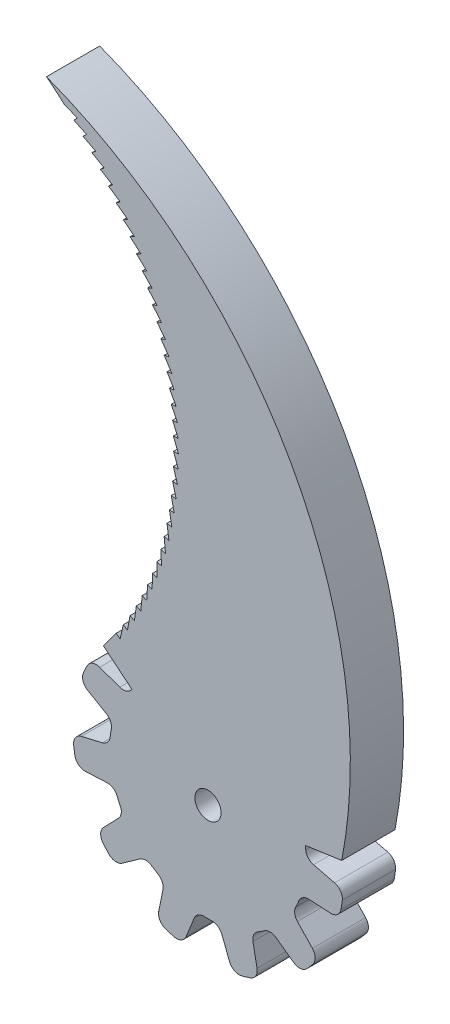
SolidWorks part; units mm, degrees
ref_plane "Plano frontal" through (0, 0, 0) normal (0, 0, 1) x (1, 0, 0)
ref_plane "Plano superior" through (0, 0, 0) normal (0, 1, 0) x (1, 0, 0)
ref_plane "Plano direito" through (0, 0, 0) normal (1, 0, 0) x (0, 0, -1)
sketch "Esboço1" plane through (0, 0, 0) normal (0, 0, 1) x (1, 0, 0)
  line L0 (-1.7292, 15.3638) -> (-1.9869, 12.7283)
  line L1 (6.8516, 13.8597) -> (5.2099, 11.782)
  line L2 (9.7799, 11.9607) -> (8.5606, 9.6439)
  line L3 (1.761, 15.3494) -> (1.9878, 12.7412)
  line L4 (13.2571, 7.9553) -> (10.7527, 7.0949)
  line L5 (14.6938, 4.7745) -> (12.4156, 3.4848)
  line L6 (15.4535, -0.4749) -> (12.8816, 0.1553)
  line L7 (14.9425, -3.9275) -> (12.3286, -3.7808)
  line L8 (12.7436, -8.7543) -> (10.9206, -6.8337)
  line L9 (10.4471, -11.3826) -> (8.3275, -9.846)
  line L10 (5.9876, -14.2543) -> (5.4924, -11.653)
  line L11 (2.6348, -15.2238) -> (1.6824, -12.7851)
  line L12 (-2.6693, -15.2286) -> (-1.6795, -12.7725)
  line L13 (-6.0141, -14.2315) -> (-5.4969, -11.6651)
  line L14 (-10.4788, -11.368) -> (-8.3183, -9.8369)
  line L15 (-12.7535, -8.7209) -> (-10.9309, -6.8415)
  line L16 (-14.9613, -3.8981) -> (-12.316, -3.7781)
  line L17 (-15.4438, -0.4414) -> (-12.8944, 0.1543)
  line L18 (-14.6937, 4.8094) -> (-12.4035, 3.4802)
  line L19 (-13.2308, 7.9782) -> (-10.7641, 7.101)
  line L20 (-9.761, 11.99) -> (-8.553, 9.6335)
  line L21 (-6.8171, 13.8648) -> (-5.2162, 11.7933)
  circle A0 centre (0, 0) radius 1.6
  arc A1 (1.9878, 12.7412) -> (2.9281, 11.6373) centre (3.2331, 12.8495) ccw
  arc A2 (0.558, 16.4904) -> (-0.5249, 16.4915) centre (0, 0) ccw
  arc A3 (0.558, 16.4904) -> (1.761, 15.3494) centre (0.5157, 15.2411) cw
  arc A4 (-0.5249, 16.4915) -> (-1.7292, 15.3638) centre (-0.4851, 15.2421) ccw
  arc A5 (-1.9869, 12.7283) -> (-2.9262, 11.6378) centre (-3.231, 12.85) cw
  arc A6 (8.5606, 9.6439) -> (8.7548, 8.2069) centre (9.6668, 9.0618) ccw
  arc A7 (9.3848, 13.571) -> (8.4744, 14.1573) centre (0, 0) ccw
  arc A8 (9.3848, 13.571) -> (9.7799, 11.9607) centre (8.6738, 12.5428) cw
  arc A9 (8.4744, 14.1573) -> (6.8516, 13.8597) centre (7.8324, 13.0848) ccw
  arc A10 (5.2099, 11.782) -> (3.8302, 11.3723) centre (4.2292, 12.5569) cw
  arc A11 (12.4156, 3.4848) -> (11.802, 2.1708) centre (13.0314, 2.397) ccw
  arc A12 (15.232, 6.3428) -> (14.7831, 7.3283) centre (0, 0) ccw
  arc A13 (15.232, 6.3428) -> (14.6938, 4.7745) centre (14.078, 5.8623) cw
  arc A14 (14.7831, 7.3283) -> (13.2571, 7.9553) centre (13.6632, 6.7731) ccw
  arc A15 (10.7527, 7.0949) -> (9.3705, 7.4963) centre (10.3466, 8.2771) cw
  arc A16 (12.3286, -3.7808) -> (11.1021, -4.5544) centre (12.2586, -5.0288) ccw
  arc A17 (16.2431, -2.8991) -> (16.3983, -1.8274) centre (0, 0) ccw
  arc A18 (16.2431, -2.8991) -> (14.9425, -3.9275) centre (15.0126, -2.6795) cw
  arc A19 (16.3983, -1.8274) -> (15.4535, -0.4749) centre (15.156, -1.689) ccw
  arc A20 (12.8816, 0.1553) -> (11.9357, 1.2402) centre (13.179, 1.3694) cw
  arc A21 (8.3275, -9.846) -> (6.8774, -9.8337) centre (7.5938, -10.858) ccw
  arc A22 (12.0972, -11.2206) -> (12.8072, -10.403) centre (0, 0) ccw
  arc A23 (12.0972, -11.2206) -> (10.4471, -11.3826) centre (11.1808, -10.3705) cw
  arc A24 (12.8072, -10.403) -> (12.7436, -8.7543) centre (11.8369, -9.6148) ccw
  arc A25 (10.9206, -6.8337) -> (10.7115, -5.4096) centre (11.8273, -5.9731) cw
  arc A26 (1.6824, -12.7851) -> (0.4691, -11.9908) centre (0.518, -13.2399) ccw
  arc A27 (4.1105, -15.9796) -> (5.1498, -15.6756) centre (0, 0) ccw
  arc A28 (4.1105, -15.9796) -> (2.6348, -15.2238) centre (3.7991, -14.769) cw
  arc A29 (5.1498, -15.6756) -> (5.9876, -14.2543) centre (4.7597, -14.488) ccw
  arc A30 (5.4924, -11.653) -> (6.0864, -10.3419) centre (6.7204, -11.4192) cw
  arc A31 (-5.4969, -11.6651) -> (-6.0881, -10.341) centre (-6.7222, -11.4181) ccw
  arc A32 (-5.1812, -15.6652) -> (-4.1426, -15.9713) centre (0, 0) ccw
  arc A33 (-5.1812, -15.6652) -> (-6.0141, -14.2315) centre (-4.7887, -14.4785) cw
  arc A34 (-4.1426, -15.9713) -> (-2.6693, -15.2286) centre (-3.8287, -14.7614) ccw
  arc A35 (-1.6795, -12.7725) -> (-0.4711, -11.9908) centre (-0.5201, -13.2398) cw
  arc A36 (-10.9309, -6.8415) -> (-10.7124, -5.4079) centre (-11.8282, -5.9712) ccw
  arc A37 (-12.828, -10.3772) -> (-12.1197, -11.1963) centre (0, 0) ccw
  arc A38 (-12.828, -10.3772) -> (-12.7535, -8.7209) centre (-11.8562, -9.5911) cw
  arc A39 (-12.1197, -11.1963) -> (-10.4788, -11.368) centre (-11.2015, -10.3481) ccw
  arc A40 (-8.3183, -9.8369) -> (-6.879, -9.8326) centre (-7.5955, -10.8568) cw
  arc A41 (-12.8944, 0.1543) -> (-11.9355, 1.2421) centre (-13.1788, 1.3715) ccw
  arc A42 (-16.402, -1.7946) -> (-16.2489, -2.8665) centre (0, 0) ccw
  arc A43 (-16.402, -1.7946) -> (-15.4438, -0.4414) centre (-15.1594, -1.6586) cw
  arc A44 (-16.2489, -2.8665) -> (-14.9613, -3.8981) centre (-15.0179, -2.6494) ccw
  arc A45 (-12.316, -3.7781) -> (-11.1029, -4.5526) centre (-12.2594, -5.0269) cw
  arc A46 (-10.7641, 7.101) -> (-9.3693, 7.4978) centre (-10.3453, 8.2788) ccw
  arc A47 (-14.7684, 7.3579) -> (-15.2192, 6.3734) centre (0, 0) ccw
  arc A48 (-14.7684, 7.3579) -> (-13.2308, 7.9782) centre (-13.6496, 6.8005) cw
  arc A49 (-15.2192, 6.3734) -> (-14.6937, 4.8094) centre (-14.0662, 5.8905) ccw
  arc A50 (-12.4035, 3.4802) -> (-11.8017, 2.1727) centre (-13.031, 2.3991) cw
  arc A51 (-5.2162, 11.7933) -> (-3.8283, 11.3729) centre (-4.2271, 12.5576) ccw
  arc A52 (-8.446, 14.1743) -> (-9.3575, 13.5898) centre (0, 0) ccw
  arc A53 (-8.446, 14.1743) -> (-6.8171, 13.8648) centre (-7.8061, 13.1004) cw
  arc A54 (-9.3575, 13.5898) -> (-9.761, 11.99) centre (-8.6486, 12.5602) ccw
  arc A55 (-8.553, 9.6335) -> (-8.7535, 8.2083) centre (-9.6653, 9.0633) cw
  arc A56 (-8.7535, 8.2083) -> (-9.3693, 7.4978) centre (0, 0) ccw
  arc A57 (-11.8017, 2.1727) -> (-11.9355, 1.2421) centre (0, 0) ccw
  arc A58 (-11.1029, -4.5526) -> (-10.7124, -5.4079) centre (0, 0) ccw
  arc A59 (-6.879, -9.8326) -> (-6.0881, -10.341) centre (0, 0) ccw
  arc A60 (-0.4711, -11.9908) -> (0.4691, -11.9908) centre (0, 0) ccw
  arc A61 (6.0864, -10.3419) -> (6.8774, -9.8337) centre (0, 0) ccw
  arc A62 (10.7115, -5.4096) -> (11.1021, -4.5544) centre (0, 0) ccw
  arc A63 (11.9357, 1.2402) -> (11.802, 2.1708) centre (0, 0) ccw
  arc A64 (9.3705, 7.4963) -> (8.7548, 8.2069) centre (0, 0) ccw
  arc A65 (3.8302, 11.3723) -> (2.9281, 11.6373) centre (0, 0) ccw
  arc A66 (-2.9262, 11.6378) -> (-3.8283, 11.3729) centre (0, 0) ccw
  point P1 (1.3394, 16.8496)
  point P6 (-1.2931, 16.8435)
  point P15 (-1.7798, 11.8673)
  point P19 (-1.5419, 16.8679)
  point P128 (-2.0286, 11.8916)
  point P130 (1.7726, 11.8684)
  point P138 (1.5885, 16.8712)
  point P139 (2.0216, 11.89)
  point P146 (0, 0)
  dimension "D1" = 1.25
  dimension "D2" = 11
extrude "Ressalto-extrusão1" add sketch "Esboço1" along normal blind 6.5
sketch "Esboço6" plane through (0, 0, 6.5) normal (0, 0, 1) x (1, 0, 0)
  line L0 (-4.7082, 41.7473) -> (-4.7062, 41.735)
  line L1 (-12.7581, 10.463) -> (-8.5055, 6.9754)
  line L2 (16.3344, 2.3306) -> (10.8897, 1.5537)
  line L3 (-16.383, 64.2477) -> (-15.9602, 64.6734)
  line L4 (-15.9602, 64.6734) -> (-17.5494, 65.3413)
  line L5 (-15.2522, 63.0997) -> (-14.8127, 63.5081)
  line L6 (-14.8127, 63.5081) -> (-16.3741, 64.239)
  line L7 (-14.1681, 61.9074) -> (-13.7127, 62.2981)
  line L8 (-13.7127, 62.2981) -> (-15.2436, 63.0906)
  line L9 (-13.1324, 60.6729) -> (-12.6618, 61.0451)
  line L10 (-12.6618, 61.0451) -> (-14.1599, 61.898)
  line L11 (-12.1468, 59.3981) -> (-11.6617, 59.7512)
  line L12 (-11.6617, 59.7512) -> (-13.1246, 60.6632)
  line L13 (-11.2128, 58.085) -> (-10.714, 58.4184)
  line L14 (-10.714, 58.4184) -> (-12.1393, 59.388)
  line L15 (-10.3319, 56.7356) -> (-9.8202, 57.0489)
  line L16 (-9.8202, 57.0489) -> (-11.2057, 58.0746)
  line L17 (-9.5055, 55.3522) -> (-8.9817, 55.6449)
  line L18 (-8.9817, 55.6449) -> (-10.3253, 56.725)
  line L19 (-8.735, 53.937) -> (-8.1999, 54.2085)
  line L20 (-8.1999, 54.2085) -> (-9.4993, 55.3414)
  line L21 (-8.0215, 52.4921) -> (-7.4761, 52.7421)
  line L22 (-7.4761, 52.7421) -> (-8.7292, 53.9259)
  line L23 (-7.3662, 51.02) -> (-6.8112, 51.248)
  line L24 (-6.8112, 51.248) -> (-8.0162, 52.4808)
  line L25 (-6.7701, 49.5228) -> (-6.2065, 49.7285)
  line L26 (-6.2065, 49.7285) -> (-7.3614, 51.0084)
  line L27 (-6.2343, 48.0031) -> (-5.6629, 48.1862)
  line L28 (-5.6629, 48.1862) -> (-6.7658, 49.5111)
  line L29 (-5.7594, 46.4633) -> (-5.1812, 46.6234)
  line L30 (-5.1812, 46.6234) -> (-6.2304, 47.9913)
  line L31 (-5.3464, 44.9057) -> (-4.7622, 45.0426)
  line L32 (-4.7622, 45.0426) -> (-5.756, 46.4512)
  line L33 (-4.9958, 43.3329) -> (-4.4066, 43.4464)
  line L34 (-4.4066, 43.4464) -> (-5.3434, 44.8935)
  line L35 (-4.7082, 41.7473) -> (-4.115, 41.8373)
  line L36 (-4.115, 41.8373) -> (-4.9933, 43.3206)
  line L37 (-4.4841, 40.1516) -> (-3.8877, 40.2178)
  line L38 (-3.8877, 40.2178) -> (-4.7062, 41.735)
  line L39 (-4.3238, 38.5481) -> (-3.7253, 38.5905)
  line L40 (-3.7253, 38.5905) -> (-4.4826, 40.1391)
  line L41 (-4.2275, 36.9396) -> (-3.6278, 36.9581)
  line L42 (-3.6278, 36.9581) -> (-4.3228, 38.5357)
  line L43 (-4.1956, 35.3285) -> (-3.5956, 35.323)
  line L44 (-3.5956, 35.323) -> (-4.2271, 36.9271)
  line L45 (-4.2278, 33.7174) -> (-3.6286, 33.688)
  line L46 (-3.6286, 33.688) -> (-4.1956, 35.316)
  line L47 (-4.3243, 32.1089) -> (-3.7267, 32.0556)
  line L48 (-3.7267, 32.0556) -> (-4.2283, 33.7049)
  line L49 (-4.4849, 30.5055) -> (-3.8899, 30.4284)
  line L50 (-3.8899, 30.4284) -> (-4.3253, 32.0964)
  line L51 (-4.7093, 28.9098) -> (-4.1179, 28.809)
  line L52 (-4.1179, 28.809) -> (-4.4864, 30.4931)
  line L53 (-4.9972, 27.3243) -> (-4.4102, 27.2)
  line L54 (-4.4102, 27.2) -> (-4.7113, 28.8974)
  line L55 (-5.3481, 25.7515) -> (-4.7665, 25.604)
  line L56 (-4.7665, 25.604) -> (-4.9997, 27.312)
  line L57 (-5.7614, 24.194) -> (-5.1862, 24.0234)
  line L58 (-5.1862, 24.0234) -> (-5.3511, 25.7394)
  line L59 (-6.2365, 22.6542) -> (-5.6686, 22.4608)
  line L60 (-5.6686, 22.4608) -> (-5.7649, 24.182)
  line L61 (-6.7727, 21.1346) -> (-6.2129, 20.9187)
  line L62 (-6.2129, 20.9187) -> (-6.2404, 22.6423)
  line L63 (-7.369, 19.6376) -> (-6.8182, 19.3995)
  line L64 (-6.8182, 19.3995) -> (-6.7771, 21.1229)
  line L65 (-8.0245, 18.1655) -> (-7.4837, 17.9057)
  line L66 (-7.4837, 17.9057) -> (-7.3738, 19.626)
  line L67 (-8.7383, 16.7208) -> (-8.2083, 16.4396)
  line L68 (-8.2083, 16.4396) -> (-8.0299, 18.1542)
  line L69 (-9.5091, 15.3057) -> (-8.9907, 15.0035)
  line L70 (-8.9907, 15.0035) -> (-8.744, 16.7097)
  line L71 (-10.3357, 13.9224) -> (-9.8298, 13.5999)
  line L72 (-9.8298, 13.5999) -> (-9.5153, 15.2948)
  line L73 (-11.2168, 12.5733) -> (-10.7242, 12.2308)
  line L74 (-10.7242, 12.2308) -> (-10.3423, 13.9118)
  line L75 (-11.2168, 12.5733) -> (-12.7581, 10.463)
  line L76 (-4.4841, 40.1516) -> (-4.4826, 40.1391)
  line L77 (-4.3238, 38.5481) -> (-4.3228, 38.5357)
  line L78 (-4.2271, 36.9271) -> (-4.2275, 36.9396)
  line L79 (-4.1956, 35.316) -> (-4.1956, 35.3285)
  line L82 (-4.3253, 32.0964) -> (-4.3243, 32.1089)
  line L83 (-4.4864, 30.4931) -> (-4.4849, 30.5055)
  line L84 (-4.7113, 28.8974) -> (-4.7093, 28.9098)
  line L85 (-4.9972, 27.3243) -> (-4.9997, 27.312)
  line L86 (-5.3511, 25.7394) -> (-5.3481, 25.7515)
  line L87 (-5.7649, 24.182) -> (-5.7614, 24.194)
  line L88 (-6.2404, 22.6423) -> (-6.2365, 22.6542)
  line L89 (-6.7727, 21.1346) -> (-6.7771, 21.1229)
  line L90 (-7.369, 19.6376) -> (-7.3738, 19.626)
  line L91 (-8.0245, 18.1655) -> (-8.0299, 18.1542)
  line L92 (-8.744, 16.7097) -> (-8.7383, 16.7208)
  line L93 (-9.5153, 15.2948) -> (-9.5091, 15.3057)
  line L94 (-10.3423, 13.9118) -> (-10.3357, 13.9224)
  line L96 (-4.2283, 33.7049) -> (-4.2278, 33.7174)
  arc A0 (-19.7213, 67.1645) -> (-17.5494, 65.3413) centre (-44.5915, 35.3321) cw
  arc A1 (-5.7594, 46.4633) -> (-5.756, 46.4512) centre (-44.5915, 35.3321) cw
  arc A2 (-19.7213, 67.1645) -> (16.3344, 2.3306) centre (-40.3263, 13.2629) cw
  circle A4 centre (0, 0) radius 11
  arc A5 (-6.2343, 48.0031) -> (-6.2304, 47.9913) centre (-44.5915, 35.3321) cw
  arc A6 (-5.3464, 44.9057) -> (-5.3434, 44.8935) centre (-44.5915, 35.3321) cw
  arc A7 (-4.9958, 43.3329) -> (-4.9933, 43.3206) centre (-44.5915, 35.3321) cw
  arc A8 (-6.7701, 49.5228) -> (-6.7658, 49.5111) centre (-44.5915, 35.3321) cw
  arc A9 (-7.3662, 51.02) -> (-7.3614, 51.0084) centre (-44.5915, 35.3321) cw
  arc A10 (-8.0215, 52.4921) -> (-8.0162, 52.4808) centre (-44.5915, 35.3321) cw
  arc A11 (-8.735, 53.937) -> (-8.7292, 53.9259) centre (-44.5915, 35.3321) cw
  arc A12 (-9.5055, 55.3522) -> (-9.4993, 55.3414) centre (-44.5915, 35.3321) cw
  arc A13 (-10.3319, 56.7356) -> (-10.3253, 56.725) centre (-44.5915, 35.3321) cw
  arc A14 (-11.2128, 58.085) -> (-11.2057, 58.0746) centre (-44.5915, 35.3321) cw
  arc A15 (-15.2522, 63.0997) -> (-15.2436, 63.0906) centre (-44.5915, 35.3321) cw
  arc A16 (-16.383, 64.2477) -> (-16.3741, 64.239) centre (-44.5915, 35.3321) cw
  arc A17 (-14.1681, 61.9074) -> (-14.1599, 61.898) centre (-44.5915, 35.3321) cw
  arc A18 (-13.1324, 60.6729) -> (-13.1246, 60.6632) centre (-44.5915, 35.3321) cw
  arc A19 (-12.1468, 59.3981) -> (-12.1393, 59.388) centre (-44.5915, 35.3321) cw
  point P124 (-44.5915, 35.3321)
  dimension "D2" = 36
  dimension "D1" = 70
extrude "Ressalto-extrusão2" add sketch "Esboço6" against normal blind 6.5
